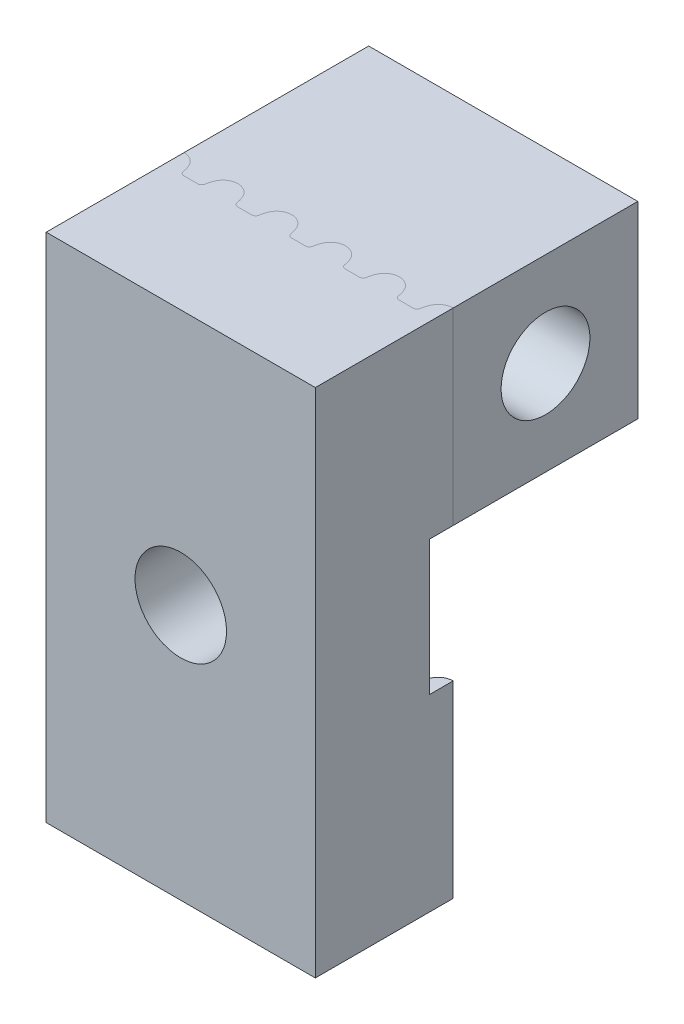
SolidWorks part; units mm, degrees
ref_plane "Front Plane" through (0, 0, 0) normal (0, 0, 1) x (1, 0, 0)
ref_plane "Top Plane" through (0, 0, 0) normal (0, 1, 0) x (1, 0, 0)
ref_plane "Right Plane" through (0, 0, 0) normal (1, 0, 0) x (0, 0, -1)
sketch "Sketch1" plane through (0, 0, 0) normal (0, 0, 1) x (1, 0, 0)
  line L1 (5, 9.5) -> (-5, 9.5)
  line L2 (5, 9.5) -> (5, -9.5)
  line L3 (5, -9.5) -> (-5, -9.5)
  line L4 (-5, 9.5) -> (-5, -9.5)
  line L5 (5, 9.5) -> (-5, -9.5) construction
  line L6 (5, -9.5) -> (-5, 9.5) construction
  point P0 (0, 0)
  dimension "D1" = 10
  dimension "D2" = 19
extrude "Boss-Extrude1" add sketch "Sketch1" along normal blind 4.25
hole_wizard "M3 Clearance Hole1" positions "Sketch3" profile "Sketch4" hole size "M3" standard "ANSI Metric" end condition through all
sketch "Sketch3" plane through (0, 0, 4.25) normal (0, 0, 1) x (1, 0, 0)
  point P0 (0, 0)
sketch "Sketch4" plane through (0, 0, 4.25) normal (1, 0, 0) x (0, -1, 0)
  line L0 (0, 0) -> (0, 4.25)
  line L1 (0, 4.25) -> (1.7, 4.25)
  line L2 (1.7, 4.25) -> (1.7, 0)
  line L5 (1.7, 0) -> (0, 0)
  line L11 (0, -6.35) -> (0, 107.95) construction
  dimension "Thru Hole Dia." = 3.4
  dimension "Thru Hole Depth" = 4.25
sketch "Sketch6" plane through (0, 9.5, 0) normal (0, 1, 0) x (1, 0, 0)
  line L0 (-5, 0) -> (-3, 0)
  line L1 (5, 0) -> (-5, 0) construction
  line L3 (-3.7421, 0.1225) -> (-4.2579, 0.1225)
  line L4 (-5, 0.1225) -> (-5, 0)
  line L5 (-5, 0.1225) -> (-5, 0.8725)
  line L6 (-4, 0) -> (-4, 0.5833) construction
  line L7 (-3, 0.1225) -> (-3, 0)
  line L8 (-3, 0.1225) -> (-3, 0.8725)
  arc A1 (-4.4065, 0.2522) -> (-4.5045, 0.5674) centre (-5.3973, 0.1171) ccw
  arc A2 (-4.5045, 0.5674) -> (-5, 0.8725) centre (-5, 0.3175) ccw
  arc A3 (-4.4065, 0.2522) -> (-4.2579, 0.1225) centre (-4.2579, 0.2725) ccw
  arc A4 (-3.5935, 0.2522) -> (-3.7421, 0.1225) centre (-3.7421, 0.2725) cw
  arc A5 (-3.5935, 0.2522) -> (-3.4955, 0.5674) centre (-2.6027, 0.1171) cw
  arc A6 (-3.4955, 0.5674) -> (-3, 0.8725) centre (-3, 0.3175) cw
  point P17 (-4, 0.1225)
  point P18 (-4, 0)
  point P25 (0, 0)
  dimension "D4" = 0.3
  dimension "D5" = 2
  dimension "D1" = 0.1225
  dimension "D2" = 1
  dimension "D3" = 0.75
  dimension "D6" = 0.1225
extrude "Boss-Extrude2" add sketch "Sketch6" against normal blind 7
pattern_linear "LPattern1" count 5 spacing 2 along (1, 0, 0) of "Boss-Extrude2"
mirror "Mirror1" about plane through (0, 0, 0) normal (0, 1, 0) of "LPattern1", "Boss-Extrude2"
sketch "Sketch7" plane through (0, -9.5, 0) normal (0, -1, 0) x (1, 0, 0)
  line L5 (-5, -0.8725) -> (-5, -5.8725)
  line L6 (5, -0.8725) -> (5, -5.8725)
  line L7 (-5, -5.8725) -> (5, -5.8725)
  line L8 (-3.7421, -0.1225) -> (-4.2579, -0.1225) construction
  line L9 (-1.7421, -0.1225) -> (-2.2579, -0.1225) construction
  line L10 (0.2579, -0.1225) -> (-0.2579, -0.1225) construction
  line L11 (2.2579, -0.1225) -> (1.7421, -0.1225) construction
  line L12 (4.2579, -0.1225) -> (3.7421, -0.1225) construction
  line L13 (-3.7421, -0.1225) -> (-4.2579, -0.1225)
  line L14 (-1.7421, -0.1225) -> (-2.2579, -0.1225)
  line L15 (0.2579, -0.1225) -> (-0.2579, -0.1225)
  line L16 (2.2579, -0.1225) -> (1.7421, -0.1225)
  line L17 (4.2579, -0.1225) -> (3.7421, -0.1225)
  arc A26 (-5, -0.8725) -> (-4.5045, -0.5674) centre (-5, -0.3175) ccw construction
  arc A27 (-4.5045, -0.5674) -> (-4.4065, -0.2522) centre (-5.3973, -0.1171) ccw construction
  arc A28 (-4.2579, -0.1225) -> (-4.4065, -0.2522) centre (-4.2579, -0.2725) ccw construction
  arc A29 (-3.5935, -0.2522) -> (-3.7421, -0.1225) centre (-3.7421, -0.2725) ccw construction
  arc A30 (-3.5935, -0.2522) -> (-3.4955, -0.5674) centre (-2.6027, -0.1171) ccw construction
  arc A31 (-3.4955, -0.5674) -> (-2.5045, -0.5674) centre (-3, -0.3175) ccw construction
  arc A32 (-2.5045, -0.5674) -> (-2.4065, -0.2522) centre (-3.3973, -0.1171) ccw construction
  arc A33 (-2.2579, -0.1225) -> (-2.4065, -0.2522) centre (-2.2579, -0.2725) ccw construction
  arc A34 (-1.5935, -0.2522) -> (-1.7421, -0.1225) centre (-1.7421, -0.2725) ccw construction
  arc A35 (-1.5935, -0.2522) -> (-1.4955, -0.5674) centre (-0.6027, -0.1171) ccw construction
  arc A36 (-1.4955, -0.5674) -> (-0.5045, -0.5674) centre (-1, -0.3175) ccw construction
  arc A37 (-0.5045, -0.5674) -> (-0.4065, -0.2522) centre (-1.3973, -0.1171) ccw construction
  arc A38 (-0.2579, -0.1225) -> (-0.4065, -0.2522) centre (-0.2579, -0.2725) ccw construction
  arc A39 (0.4065, -0.2522) -> (0.2579, -0.1225) centre (0.2579, -0.2725) ccw construction
  arc A40 (0.4065, -0.2522) -> (0.5045, -0.5674) centre (1.3973, -0.1171) ccw construction
  arc A41 (0.5045, -0.5674) -> (1.4955, -0.5674) centre (1, -0.3175) ccw construction
  arc A42 (1.4955, -0.5674) -> (1.5935, -0.2522) centre (0.6027, -0.1171) ccw construction
  arc A43 (1.7421, -0.1225) -> (1.5935, -0.2522) centre (1.7421, -0.2725) ccw construction
  arc A44 (2.4065, -0.2522) -> (2.2579, -0.1225) centre (2.2579, -0.2725) ccw construction
  arc A45 (2.4065, -0.2522) -> (2.5045, -0.5674) centre (3.3973, -0.1171) ccw construction
  arc A46 (2.5045, -0.5674) -> (3.4955, -0.5674) centre (3, -0.3175) ccw construction
  arc A47 (3.4955, -0.5674) -> (3.5935, -0.2522) centre (2.6027, -0.1171) ccw construction
  arc A48 (3.7421, -0.1225) -> (3.5935, -0.2522) centre (3.7421, -0.2725) ccw construction
  arc A49 (4.4065, -0.2522) -> (4.2579, -0.1225) centre (4.2579, -0.2725) ccw construction
  arc A50 (4.4065, -0.2522) -> (4.5045, -0.5674) centre (5.3973, -0.1171) ccw construction
  arc A51 (4.5045, -0.5674) -> (5, -0.8725) centre (5, -0.3175) ccw construction
  arc A52 (-5, -0.8725) -> (-4.5045, -0.5674) centre (-5, -0.3175) ccw
  arc A53 (-4.5045, -0.5674) -> (-4.4065, -0.2522) centre (-5.3973, -0.1171) ccw
  arc A54 (-4.2579, -0.1225) -> (-4.4065, -0.2522) centre (-4.2579, -0.2725) ccw
  arc A55 (-3.5935, -0.2522) -> (-3.7421, -0.1225) centre (-3.7421, -0.2725) ccw
  arc A56 (-3.5935, -0.2522) -> (-3.4955, -0.5674) centre (-2.6027, -0.1171) ccw
  arc A57 (-3.4955, -0.5674) -> (-2.5045, -0.5674) centre (-3, -0.3175) ccw
  arc A58 (-2.5045, -0.5674) -> (-2.4065, -0.2522) centre (-3.3973, -0.1171) ccw
  arc A59 (-2.2579, -0.1225) -> (-2.4065, -0.2522) centre (-2.2579, -0.2725) ccw
  arc A60 (-1.5935, -0.2522) -> (-1.7421, -0.1225) centre (-1.7421, -0.2725) ccw
  arc A61 (-1.5935, -0.2522) -> (-1.4955, -0.5674) centre (-0.6027, -0.1171) ccw
  arc A62 (-1.4955, -0.5674) -> (-0.5045, -0.5674) centre (-1, -0.3175) ccw
  arc A63 (-0.5045, -0.5674) -> (-0.4065, -0.2522) centre (-1.3973, -0.1171) ccw
  arc A64 (-0.2579, -0.1225) -> (-0.4065, -0.2522) centre (-0.2579, -0.2725) ccw
  arc A65 (0.4065, -0.2522) -> (0.2579, -0.1225) centre (0.2579, -0.2725) ccw
  arc A66 (0.4065, -0.2522) -> (0.5045, -0.5674) centre (1.3973, -0.1171) ccw
  arc A67 (0.5045, -0.5674) -> (1.4955, -0.5674) centre (1, -0.3175) ccw
  arc A68 (1.4955, -0.5674) -> (1.5935, -0.2522) centre (0.6027, -0.1171) ccw
  arc A69 (1.7421, -0.1225) -> (1.5935, -0.2522) centre (1.7421, -0.2725) ccw
  arc A70 (2.4065, -0.2522) -> (2.2579, -0.1225) centre (2.2579, -0.2725) ccw
  arc A71 (2.4065, -0.2522) -> (2.5045, -0.5674) centre (3.3973, -0.1171) ccw
  arc A72 (2.5045, -0.5674) -> (3.4955, -0.5674) centre (3, -0.3175) ccw
  arc A73 (3.4955, -0.5674) -> (3.5935, -0.2522) centre (2.6027, -0.1171) ccw
  arc A74 (3.7421, -0.1225) -> (3.5935, -0.2522) centre (3.7421, -0.2725) ccw
  arc A75 (4.4065, -0.2522) -> (4.2579, -0.1225) centre (4.2579, -0.2725) ccw
  arc A76 (4.4065, -0.2522) -> (4.5045, -0.5674) centre (5.3973, -0.1171) ccw
  arc A77 (4.5045, -0.5674) -> (5, -0.8725) centre (5, -0.3175) ccw
  dimension "D1" = 5
extrude "Boss-Extrude4" add sketch "Sketch7" against normal up to surface (19 mm away) separate body up to face at (0, 9.5, -0.1114)
sketch "Sketch8" plane through (0, 0, -0.1225) normal (0, 0, 1) x (1, 0, 0)
  line L0 (-5, 9.5) -> (-5, -9.5) construction
  line L1 (5, 2.5) -> (-5, 2.5)
  line L2 (5, 2.5) -> (5, -2.5)
  line L3 (5, -2.5) -> (-5, -2.5)
  line L4 (-5, 2.5) -> (-5, -2.5)
  line L5 (5, 2.5) -> (-5, -2.5) construction
  line L6 (5, -2.5) -> (-5, 2.5) construction
  line L7 (-0.5045, 9.5) -> (-1.4955, 9.5) construction
  point P0 (0, 0)
  dimension "D1" = 7
extrude "Cut-Extrude1" cut sketch "Sketch8" against normal blind 0.75
hole_wizard "M3 Clearance Hole2" positions "Sketch10" profile "Sketch11" hole size "M3" standard "ANSI Metric" end condition through all
sketch "Sketch10" plane through (0, 0, -0.8725) normal (0, 0, 1) x (1, 0, 0)
  point P0 (0, 0)
sketch "Sketch11" plane through (0, 0, -0.8725) normal (1, 0, 0) x (0, -1, 0)
  line L0 (0, 0) -> (0, 5)
  line L1 (0, 5) -> (1.7, 5)
  line L2 (1.7, 5) -> (1.7, 0)
  line L5 (1.7, 0) -> (0, 0)
  line L11 (0, -6.35) -> (0, 107.95) construction
  dimension "Thru Hole Dia." = 3.4
  dimension "Thru Hole Depth" = 5
sketch "Sketch12" plane through (0, 0, -0.1225) normal (0, 0, 1) x (1, 0, 0)
  line L1 (-5, 2.5) -> (5, 2.5)
  line L2 (-5, 2.5) -> (-5, -9.5)
  line L3 (-5, -9.5) -> (5, -9.5)
  line L4 (5, 2.5) -> (5, -9.5)
extrude "Cut-Extrude2" cut sketch "Sketch12" against normal up to next (5.75 mm away)
sketch "Sketch13" plane through (0, 0, -5.8725) normal (0, 0, -1) x (-1, 0, 0)
  line L4 (-5, 2.5) -> (5, 2.5)
  line L5 (5, 2.5) -> (5, 9.5)
  line L6 (5, 9.5) -> (-5, 9.5)
  line L7 (-5, 9.5) -> (-5, 2.5)
  line L8 (-5, 2.5) -> (5, 2.5)
  line L9 (5, 2.5) -> (5, 9.5)
  line L10 (5, 9.5) -> (-5, 9.5)
  line L11 (-5, 9.5) -> (-5, 2.5)
  dimension "D1" = 0
extrude "Boss-Extrude5" add sketch "Sketch13" along normal blind 1.86
sketch "Sketch14" plane through (-5, 0, 0) normal (-1, 0, 0) x (0, 0, 1)
  line L0 (-4.3025, 9.5) -> (-4.3025, 2.5) construction
  line L1 (-7.7325, 9.5) -> (-0.8725, 9.5) construction
  line L2 (-7.7325, 2.5) -> (-0.8725, 2.5) construction
  line L3 (-7.7325, 6) -> (-0.8725, 6) construction
  line L4 (-7.7325, 2.5) -> (-7.7325, 9.5) construction
  line L5 (-0.8725, 9.5) -> (-0.8725, 2.5) construction
  circle A0 centre (-4.3025, 6) radius 2.35
  dimension "D1" = 4.7
extrude "Cut-Extrude3" cut sketch "Sketch14" against normal blind 3.8
sketch "Sketch15" plane through (-1.2, 0, 0) normal (-1, 0, 0) x (0, 0, 1)
  circle A0 centre (-4.3025, 6) radius 1.65
  dimension "D1" = 3.3
extrude "Cut-Extrude4" cut sketch "Sketch15" against normal through all
